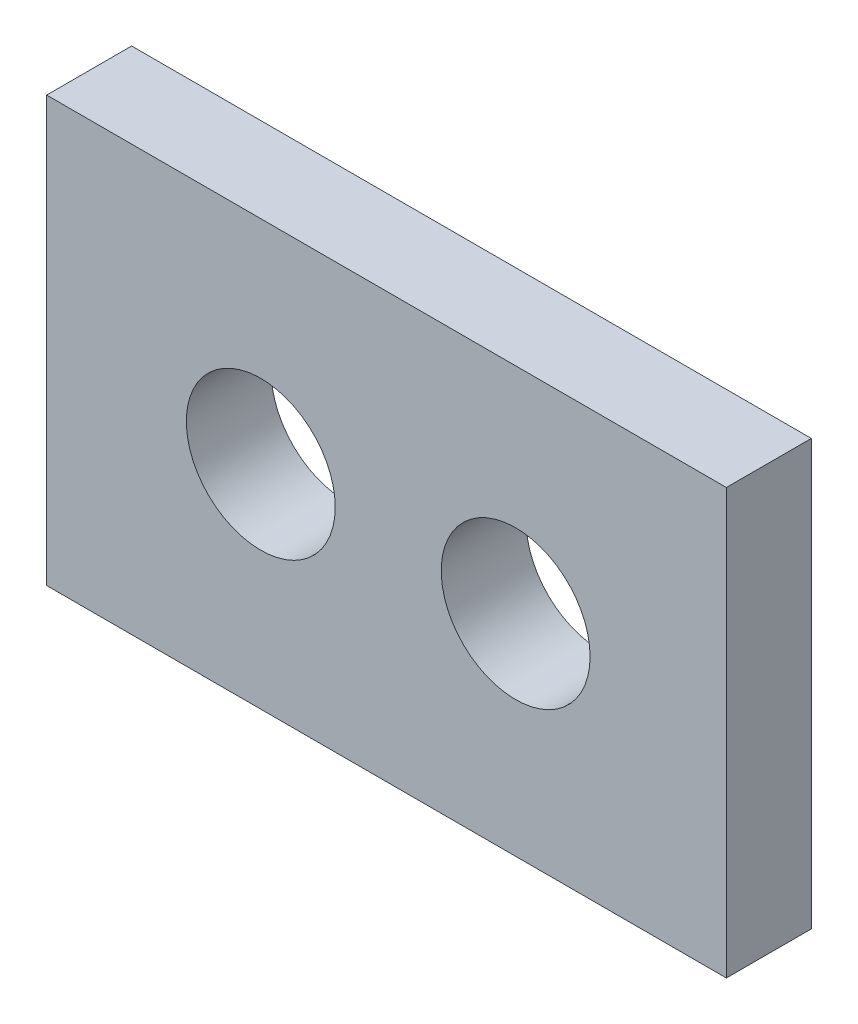
SolidWorks part; units mm, degrees
ref_plane "Front" through (0, 0, 0) normal (0, 0, 1) x (1, 0, 0)
ref_plane "Top" through (0, 0, 0) normal (0, 1, 0) x (1, 0, 0)
ref_plane "Right" through (0, 0, 0) normal (1, 0, 0) x (0, 0, -1)
sketch "草图1" plane through (0, 0, 0) normal (0, 0, 1) x (1, 0, 0)
  line L1 (0, 0) -> (16, 0)
  line L2 (0, 0) -> (0, 10)
  line L3 (0, 10) -> (16, 10)
  line L4 (16, 0) -> (16, 10)
  circle A0 centre (5.0401, 4.9928) radius 1.7525
  circle A1 centre (11.0399, 4.9473) radius 1.7525
  dimension "D1" = 6
extrude "凸台-拉伸1" add sketch "草图1" along normal blind 2
